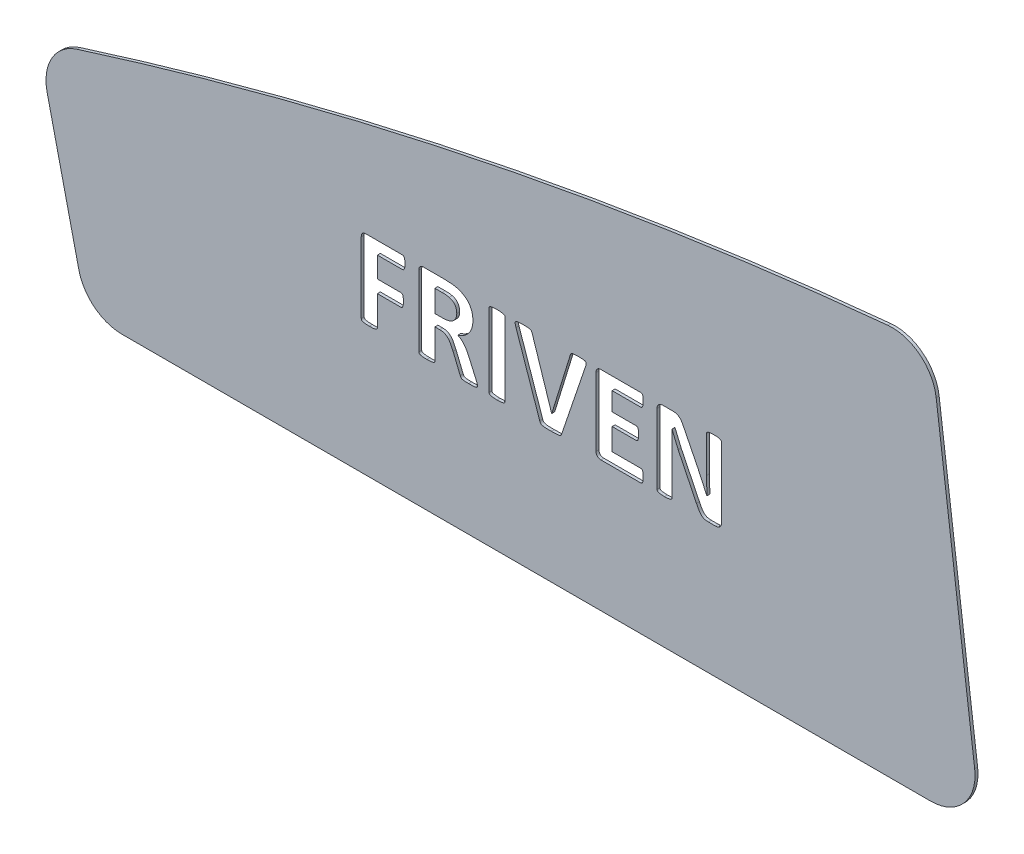
SolidWorks part; units mm, degrees
ref_plane "Plano frontal" through (0, 0, 0) normal (0, 0, 1) x (1, 0, 0)
ref_plane "Plano superior" through (0, 0, 0) normal (0, 1, 0) x (1, 0, 0)
ref_plane "Plano direito" through (0, 0, 0) normal (1, 0, 0) x (0, 0, -1)
sketch "Esboço1" plane through (0, 0, 0) normal (0, 0, 1) x (1, 0, 0)
  line L2 (94.4446, 61.6676) -> (367.7769, 61.6676)
  line L3 (382.6566, 78.5635) -> (369.642, 180.7086)
  line L5 (69.1131, 119.8406) -> (79.827, 73.3024)
  arc A0 (79.1945, 137.5034) -> (69.1131, 119.8406) centre (83.7308, 123.2058) ccw
  arc A1 (369.642, 180.7086) -> (353.3301, 193.7442) centre (354.7623, 178.8127) ccw
  arc A2 (367.7769, 61.6676) -> (382.6566, 78.5635) centre (367.7769, 76.6676) ccw
  arc A3 (79.827, 73.3024) -> (94.4446, 61.6676) centre (94.4446, 76.6676) ccw
  spline S0 degree 3 poles (79.1945, 137.5034) (169.3842, 166.1184) (260.7628, 184.8653) (353.3301, 193.7442) knots 0.031643 0.031643 0.031643 0.031643 0.681355 0.681355 0.681355 0.681355
extrude "Ressalto-extrusão1" add sketch "Esboço1" along normal blind 1
sketch "Esboço2" plane through (0, 0, 1) normal (0, 0, 1) x (1, 0, 0)
  text T0 "FRIVEN" font "Calibri" height in points 100
extrude "Corte-extrusão1" cut sketch "Esboço2" against normal through all
